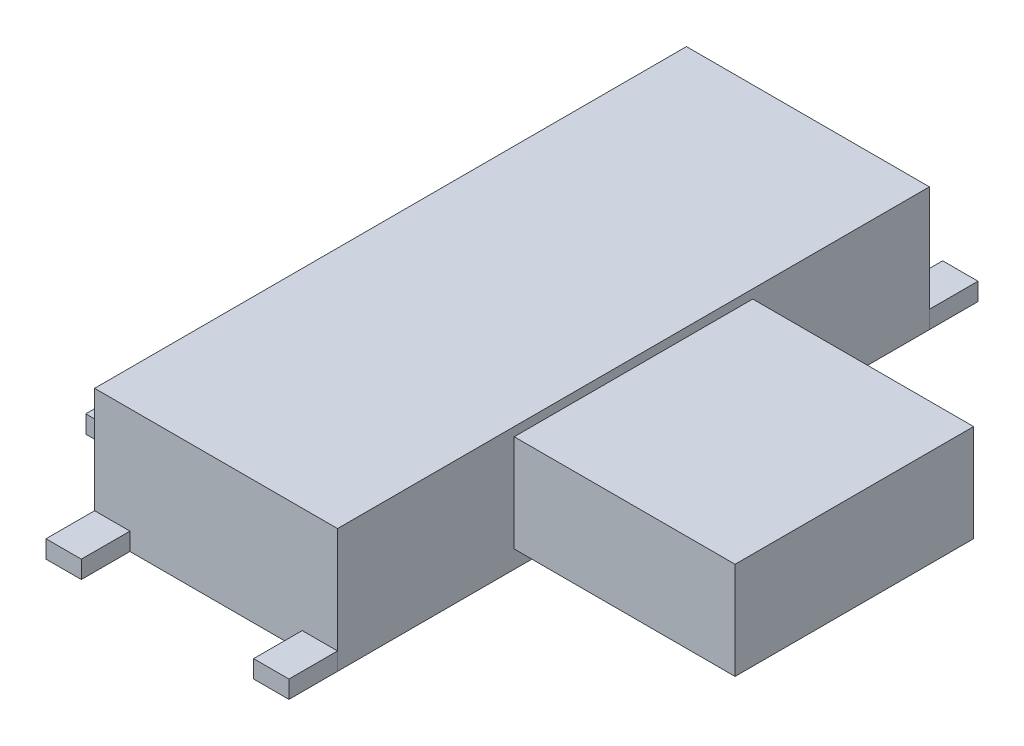
SolidWorks part; units mm, degrees
ref_plane "前视基准面" through (0, 0, 0) normal (0, 0, 1) x (1, 0, 0)
ref_plane "上视基准面" through (0, 0, 0) normal (0, 1, 0) x (1, 0, 0)
ref_plane "右视基准面" through (0, 0, 0) normal (1, 0, 0) x (0, 0, -1)
sketch "草图1" plane through (0, 0, 0) normal (0, 1, 0) x (1, 0, 0)
  line L1 (-1.375, 3.35) -> (1.375, 3.35)
  line L2 (-1.375, 3.35) -> (-1.375, -3.35)
  line L3 (-1.375, -3.35) -> (1.375, -3.35)
  line L4 (1.375, 3.35) -> (1.375, -3.35)
  line L5 (-1.375, 3.35) -> (1.375, -3.35) construction
  line L6 (-1.375, -3.35) -> (1.375, 3.35) construction
  point P0 (0, 0)
  dimension "D1" = 2.75
  dimension "D2" = 6.7
extrude "凸台-拉伸1" add sketch "草图1" along normal blind 1.4
sketch "草图2" plane through (0, 0, 0) normal (0, -1, 0) x (1, 0, 0)
  line L0 (0, 1.5) -> (0, -1.5) construction
  line L1 (-1.375, -3.35) -> (-1.375, 3.35) construction
  circle A0 centre (0, 1.5) radius 0.35
  circle A1 centre (0, -1.5) radius 0.35
  point P4 (0, 0)
  dimension "D1" = 0.7
  dimension "D2" = 3
extrude "凸台-拉伸2" add sketch "草图2" along normal blind 0.5
sketch "草图4" plane through (0, 0, 0) normal (0, 1, 0) x (1, 0, 0)
  line L5 (-1.375, 2.45) -> (-2.375, 2.45)
  line L6 (-1.375, 2.45) -> (-1.375, 2.05)
  line L7 (-1.375, 2.05) -> (-2.375, 2.05)
  line L8 (-2.375, 2.45) -> (-2.375, 2.05)
  line L9 (-1.375, -2.05) -> (-2.375, -2.05)
  line L10 (-1.375, -2.05) -> (-1.375, -2.45)
  line L11 (-1.375, -2.45) -> (-2.375, -2.45)
  line L12 (-2.375, -2.05) -> (-2.375, -2.45)
  line L13 (-1.375, 0.95) -> (-2.375, 0.95)
  line L14 (-1.375, 0.95) -> (-1.375, 0.55)
  line L15 (-1.375, 0.55) -> (-2.375, 0.55)
  line L16 (-2.375, 0.95) -> (-2.375, 0.55)
  line L17 (-1.375, 3.35) -> (-1.375, -3.35) construction
  line L18 (-2.375, 2.25) -> (-2.375, 0.75) construction
  line L19 (-2.375, 0.75) -> (-2.375, -2.25) construction
  line L20 (-1.375, 2.25) -> (-2.375, -2.25) construction
  line L22 (-1.375, 3.35) -> (-0.975, 3.35)
  line L23 (-1.375, 3.35) -> (-1.375, 3.9)
  line L24 (-1.375, 3.9) -> (-0.975, 3.9)
  line L25 (-0.975, 3.35) -> (-0.975, 3.9)
  line L26 (1.375, 3.35) -> (0.975, 3.35)
  line L27 (1.375, 3.35) -> (1.375, 3.9)
  line L28 (1.375, 3.9) -> (0.975, 3.9)
  line L29 (0.975, 3.35) -> (0.975, 3.9)
  line L30 (-1.375, -3.35) -> (-0.975, -3.35)
  line L31 (-1.375, -3.35) -> (-1.375, -3.9)
  line L32 (-1.375, -3.9) -> (-0.975, -3.9)
  line L33 (-0.975, -3.35) -> (-0.975, -3.9)
  line L34 (1.375, -3.35) -> (0.975, -3.35)
  line L35 (1.375, -3.35) -> (1.375, -3.9)
  line L36 (1.375, -3.9) -> (0.975, -3.9)
  line L37 (0.975, -3.35) -> (0.975, -3.9)
  point P18 (-1.875, 0)
  dimension "D1" = 1
  dimension "D2" = 0.4
  dimension "D3" = 1.5
  dimension "D4" = 3
  dimension "D5" = 0.55
  dimension "D6" = 0.4
extrude "凸台-拉伸4" add sketch "草图4" along normal blind 0.2 separate body
sketch "草图3" plane through (1.375, 0, 0) normal (1, 0, 0) x (0, 0, -1)
  line L0 (-3.35, 1.4) -> (3.35, 1.4) construction
  line L5 (1.35, 1.3) -> (-0.25, 1.3)
  line L6 (1.35, 1.3) -> (1.35, 0.2)
  line L7 (1.35, 0.2) -> (-0.25, 0.2)
  line L8 (-0.25, 1.3) -> (-0.25, 0.2)
  line L9 (0.55, 1.4) -> (0.55, -49998.6) construction
  line L10 (3.35, 1.4) -> (3.35, 0) construction
  point P7 (0.55, 1.3)
  dimension "D1" = 1.1
  dimension "D2" = 1.6
  dimension "D3" = 0.1
  dimension "D4" = 2
extrude "凸台-拉伸3" add sketch "草图3" along normal blind 2.5
mirror "镜向1" about plane through (0, 0, 0) normal (0, 0, 1) of "凸台-拉伸3"
